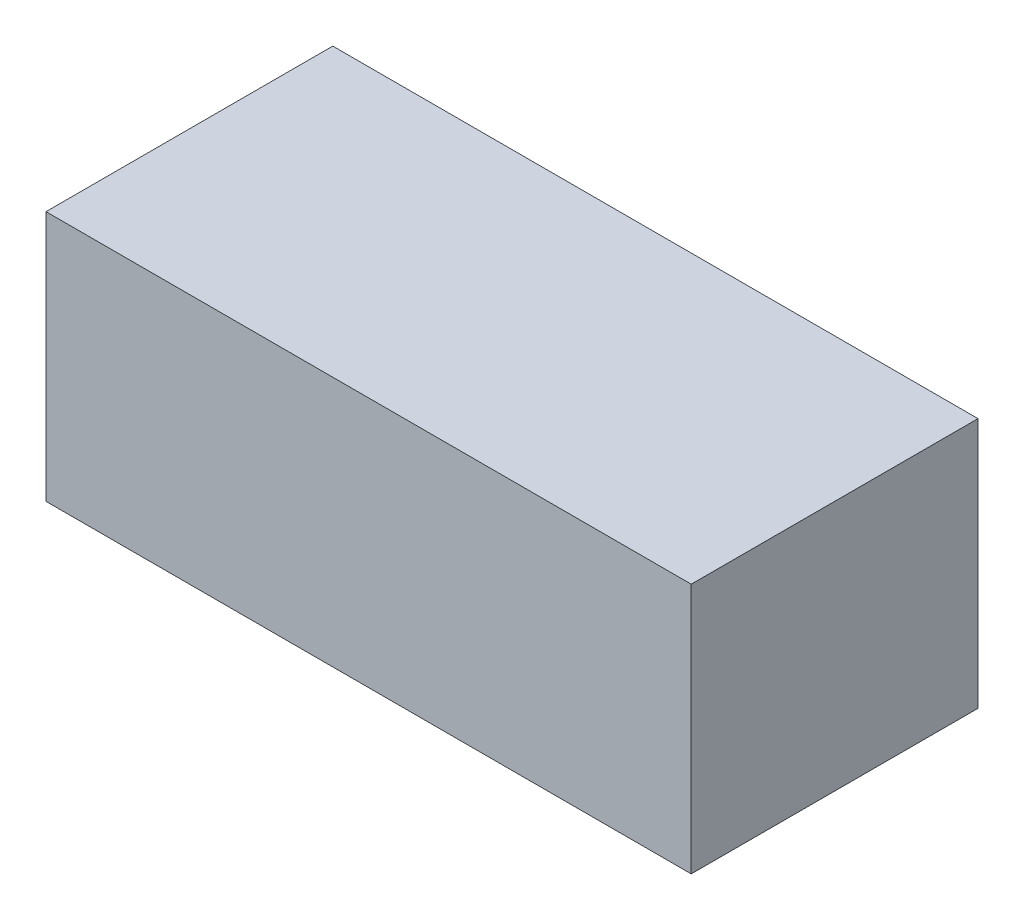
SolidWorks part; units mm, degrees
ref_plane "前基準面" through (0, 0, 0) normal (0, 0, 1) x (1, 0, 0)
ref_plane "上基準面" through (0, 0, 0) normal (0, 1, 0) x (1, 0, 0)
ref_plane "右基準面" through (0, 0, 0) normal (1, 0, 0) x (0, 0, -1)
sketch "草圖1" plane through (0, 0, 0) normal (0, 0, 1) x (1, 0, 0)
  line L1 (-68.1823, 22.2069) -> (111.8177, 22.2069)
  line L2 (-68.1823, 22.2069) -> (-68.1823, -47.7931)
  line L3 (-68.1823, -47.7931) -> (111.8177, -47.7931)
  line L4 (111.8177, 22.2069) -> (111.8177, -47.7931)
  dimension "D1" = 180
  dimension "D2" = 70
extrude "填料-伸長1" add sketch "草圖1" along normal blind 80
